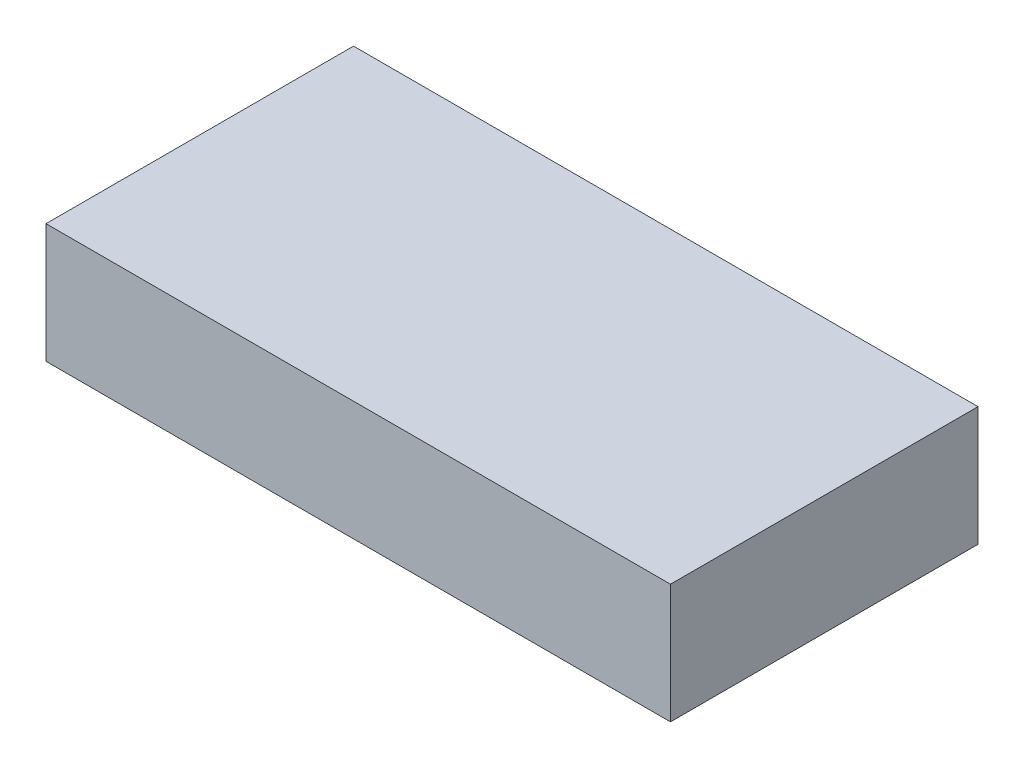
SolidWorks part; units mm, degrees
ref_plane "Front Plane" through (0, 0, 0) normal (0, 0, 1) x (1, 0, 0)
ref_plane "Top Plane" through (0, 0, 0) normal (0, 1, 0) x (1, 0, 0)
ref_plane "Right Plane" through (0, 0, 0) normal (1, 0, 0) x (0, 0, -1)
sketch "Sketch1" plane through (0, 0, 0) normal (0, 1, 0) x (1, 0, 0)
  line L1 (-99.5, -49) -> (99.5, -49)
  line L2 (-99.5, -49) -> (-99.5, 49)
  line L3 (-99.5, 49) -> (99.5, 49)
  line L4 (99.5, -49) -> (99.5, 49)
  line L5 (-99.5, -49) -> (99.5, 49) construction
  line L6 (-99.5, 49) -> (99.5, -49) construction
  point P0 (0, 0)
  dimension "D1" = 199
  dimension "D2" = 98
extrude "Boss-Extrude1" add sketch "Sketch1" along normal mid plane 38
